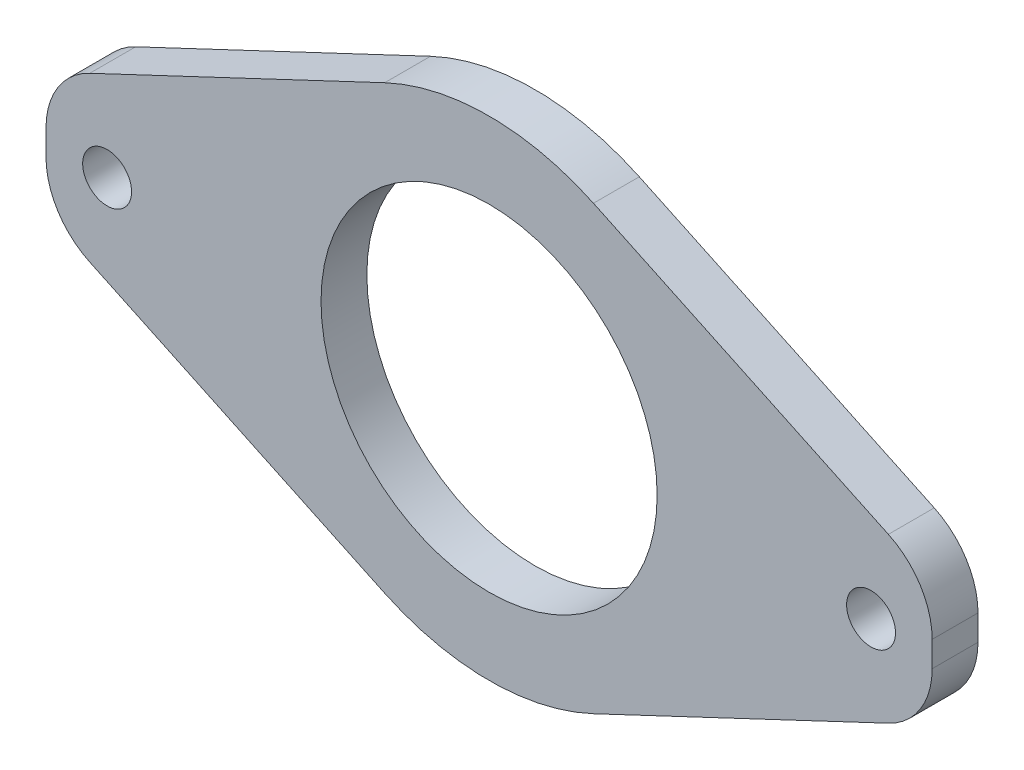
SolidWorks part; units mm, degrees
material "MDF"
ref_plane "Plano frontal" through (0, 0, 0) normal (0, 0, 1) x (1, 0, 0)
ref_plane "Plano superior" through (0, 0, 0) normal (0, 1, 0) x (1, 0, 0)
ref_plane "Plano direito" through (0, 0, 0) normal (1, 0, 0) x (0, 0, -1)
sketch "Esboço1" plane through (0, 0, 0) normal (0, 0, 1) x (1, 0, 0)
  line L0 (-19.5214, 0) -> (-12, 0) construction
  line L1 (-25, 0) -> (25, 0) construction
  line L2 (-29, 4) -> (-15.4919, 4)
  line L3 (0, 0) -> (0, 11) construction
  line L4 (29, 4) -> (15.4919, 4)
  line L5 (29, -4) -> (15.4919, -4)
  line L6 (-29, -4) -> (-15.4919, -4)
  line L7 (-29, -4) -> (-29, 4)
  line L8 (29, 4) -> (29, -4)
  line L9 (-29, -4) -> (-6.832, -14.468)
  line L10 (-29, 4) -> (-6.832, 14.468)
  line L11 (29, 4) -> (6.832, 14.468)
  line L12 (29, -4) -> (6.832, -14.468)
  circle A0 centre (0, 0) radius 11
  circle A1 centre (0, 0) radius 12 construction
  circle A3 centre (-25, 0) radius 1.6
  circle A4 centre (25, 0) radius 1.6
  arc A5 (-15.4919, 4) -> (15.4919, 4) centre (0, 0) cw
  arc A6 (-15.4919, -4) -> (15.4919, -4) centre (0, 0) ccw
  circle A7 centre (-13.5, 0) radius 3 construction
  point P5 (-12, 0)
  point P6 (-19.5214, 0)
  point P18 (0, 16)
  point P22 (0, 12)
  point P23 (0, 11)
  dimension "D1" = 22
  dimension "D2" = 24
  dimension "D3" = 3.2
  dimension "D7" = 5
  dimension "D4" = 6
  dimension "D8" = 27
  dimension "D5" = 4
  dimension "D6" = 4
  dimension "D9" = 50
extrude "Ressalto-extrusão1" add sketch "Esboço1" along normal blind 3 contours A6 L6 L9 | L6 A6 L5 L8 L4 A5 L2 L7 A0 A3 A4 | L2 A5 L10 | A6 L12 L5 | L11 A5 L4
fillet "Filete1" radius 5 4 edges at (29, 4, 1.5) (29, -4, 1.5) (-29, 4, 1.5) (-29, -4, 1.5)
